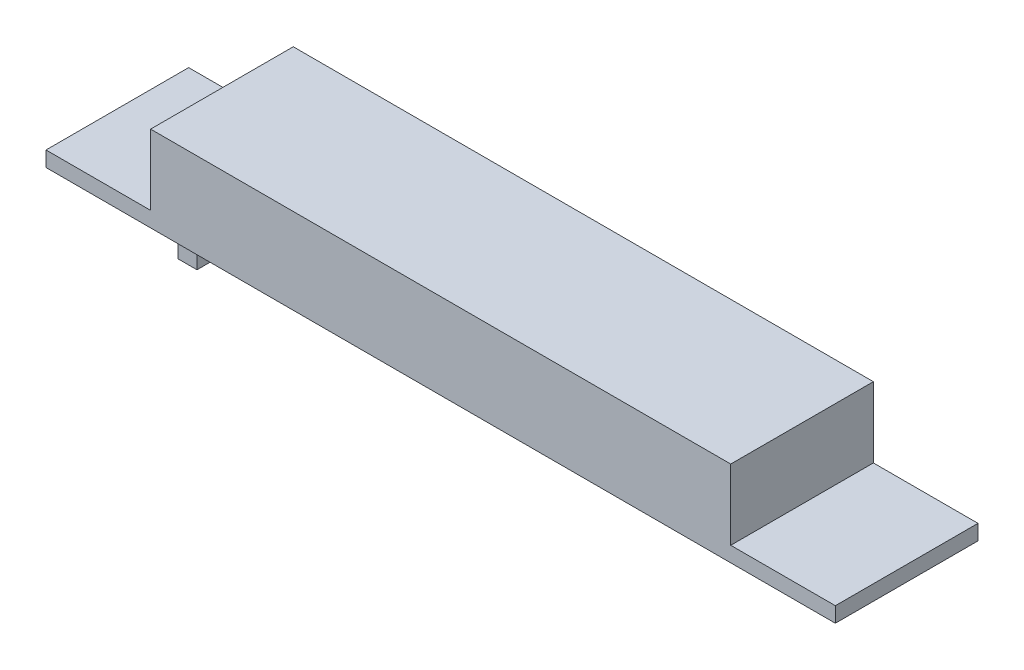
SolidWorks part; units mm, degrees
ref_plane "Front Plane" through (0, 0, 0) normal (0, 0, 1) x (1, 0, 0)
ref_plane "Top Plane" through (0, 0, 0) normal (0, 1, 0) x (1, 0, 0)
ref_plane "Right Plane" through (0, 0, 0) normal (1, 0, 0) x (0, 0, -1)
sketch "Sketch1" plane through (0, 0, 0) normal (0, 1, 0) x (1, 0, 0)
  line L1 (-41.5, -7.5) -> (41.5, -7.5)
  line L2 (-41.5, -7.5) -> (-41.5, 7.5)
  line L3 (-41.5, 7.5) -> (41.5, 7.5)
  line L4 (41.5, -7.5) -> (41.5, 7.5)
  line L5 (-41.5, -7.5) -> (41.5, 7.5) construction
  line L6 (-41.5, 7.5) -> (41.5, -7.5) construction
  point P0 (0, 0)
  dimension "D1" = 83
  dimension "D2" = 15
extrude "Boss-Extrude1" add sketch "Sketch1" along normal blind 1.6
sketch "Sketch2" plane through (0, 1.6, 0) normal (0, 1, 0) x (1, 0, 0)
  line L0 (41.5, 7.5) -> (-41.5, 7.5) construction
  line L1 (-30.5, -7.5) -> (30.5, -7.5)
  line L2 (-30.5, -7.5) -> (-30.5, 7.5)
  line L3 (-30.5, 7.5) -> (30.5, 7.5)
  line L4 (30.5, -7.5) -> (30.5, 7.5)
  line L5 (-30.5, -7.5) -> (30.5, 7.5) construction
  line L6 (-30.5, 7.5) -> (30.5, -7.5) construction
  line L7 (-41.5, -7.5) -> (41.5, -7.5) construction
  point P0 (0, 0)
  point P9 (0, 0)
  point P10 (0, 0)
  point P11 (0, 0)
  dimension "D1" = 61
extrude "Boss-Extrude2" add sketch "Sketch2" along normal blind 7.4
sketch "Sketch3" plane through (0, 0, 0) normal (0, -1, 0) x (-1, 0, 0)
  line L1 (26.5, 6.625) -> (28.5, 6.625)
  line L2 (26.5, 6.625) -> (26.5, -6.625)
  line L3 (26.5, -6.625) -> (28.5, -6.625)
  line L4 (28.5, 6.625) -> (28.5, -6.625)
  line L5 (26.5, 6.625) -> (28.5, -6.625) construction
  line L6 (26.5, -6.625) -> (28.5, 6.625) construction
  line L8 (30.5, 7.5) -> (30.5, -7.5) construction
  point P0 (27.5, 0)
  point P5 (0, 0)
  dimension "D1" = 13.25
  dimension "D2" = 2
  dimension "D3" = 2
extrude "Boss-Extrude3" add sketch "Sketch3" along normal blind 2.25
